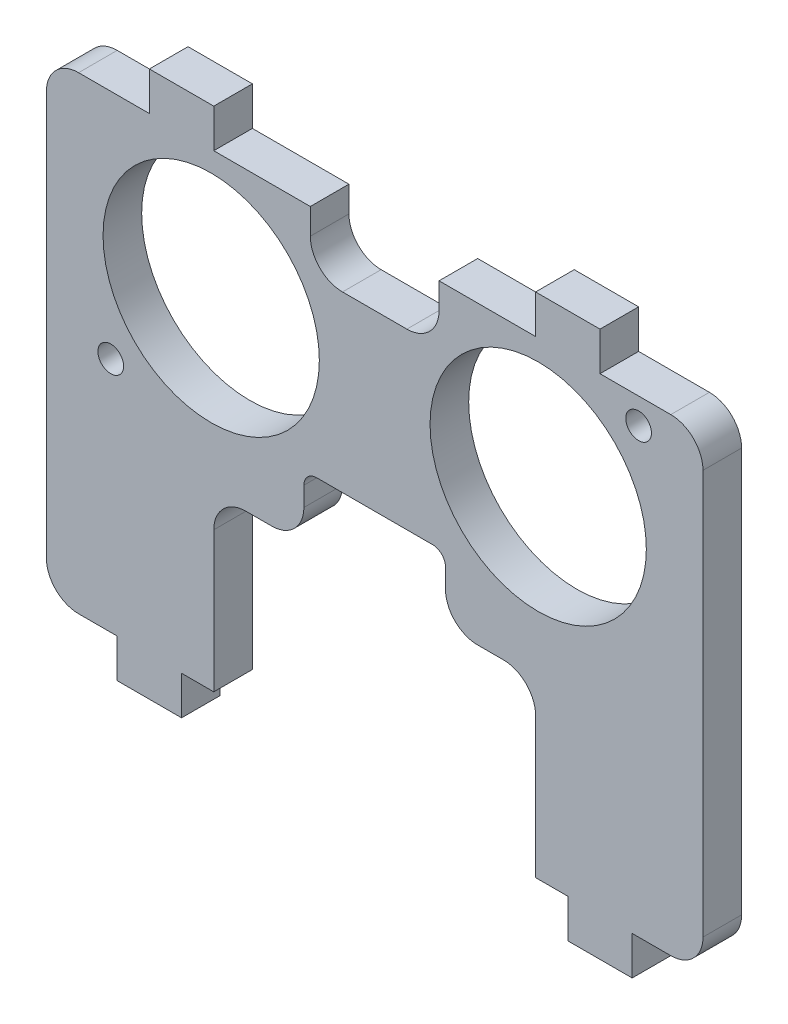
SolidWorks part; units mm, degrees
material "Beech"
ref_plane "Front Plane" through (0, 0, 0) normal (0, 0, 1) x (1, 0, 0)
ref_plane "Top Plane" through (0, 0, 0) normal (0, 1, 0) x (1, 0, 0)
ref_plane "Right Plane" through (0, 0, 0) normal (1, 0, 0) x (0, 0, -1)
sketch "Sketch1" plane through (0, 0, 0) normal (0, 0, 1) x (1, 0, 0)
  line L0 (-20.667, -16.4) -> (-20.667, 20)
  line L1 (-20.667, 20) -> (-15.667, 20)
  line L2 (24.333, 20) -> (24.333, -16.4)
  line L3 (24.333, -16.4) -> (21.833, -16.4)
  line L4 (14.333, -16.4) -> (14.333, -1)
  line L5 (13.333, 0) -> (7.333, 0)
  line L6 (-10.667, -1) -> (-10.667, -16.4)
  line L7 (-10.667, -16.4) -> (-13.167, -16.4)
  line L8 (1.833, 35.1) -> (1.833, -30.9857) construction
  line L9 (14.533, 10) -> (-10.867, 10) construction
  line L10 (-3.167, 20) -> (-3.167, 15.5)
  line L11 (-3.167, 15.5) -> (6.833, 15.5)
  line L12 (6.833, 15.5) -> (6.833, 20)
  line L13 (6.833, 20) -> (14.333, 20)
  line L14 (-20.667, 20) -> (24.333, 20) construction
  line L15 (-3.667, 2) -> (-3.667, 0)
  line L16 (-3.667, 2) -> (7.333, 2)
  line L17 (7.333, 2) -> (7.333, 0)
  line L18 (-3.667, 0) -> (-9.667, 0)
  line L19 (21.833, -16.4) -> (21.833, -19.4)
  line L20 (21.833, -19.4) -> (16.833, -19.4)
  line L21 (16.833, -19.4) -> (16.833, -16.4)
  line L22 (16.833, -16.4) -> (14.333, -16.4)
  line L23 (-18.167, -16.4) -> (-18.167, -19.4)
  line L24 (-13.167, -19.4) -> (-13.167, -16.4)
  line L25 (-18.167, -19.4) -> (-13.167, -19.4)
  line L26 (-18.167, -16.4) -> (-20.667, -16.4)
  line L27 (-15.667, 20) -> (-15.667, 23)
  line L28 (-15.667, 23) -> (-10.667, 23)
  line L29 (-10.667, 23) -> (-10.667, 20)
  line L30 (14.333, 23) -> (14.333, 20)
  line L31 (19.333, 23) -> (14.333, 23)
  line L32 (19.333, 20) -> (19.333, 23)
  line L33 (-10.667, 20) -> (-3.167, 20)
  line L34 (19.333, 20) -> (24.333, 20)
  circle A0 centre (22.333, 18) radius 1
  circle A1 centre (-18.667, 2) radius 1
  circle A2 centre (-10.867, 10) radius 8.4
  circle A3 centre (14.533, 10) radius 8.4
  arc A8 (13.333, 0) -> (14.333, -1) centre (13.333, -1) cw
  arc A9 (-9.667, 0) -> (-10.667, -1) centre (-9.667, -1) ccw
  point P21 (1.833, 10)
  point P24 (1.833, 15.5)
  point P29 (6.833, 15.5)
  point P32 (-3.167, 15.5)
  point P34 (-3.167, 20)
  point P37 (6.833, 20)
  point P42 (1.833, 20)
  point P47 (1.833, 2)
  point P53 (-3.667, 2)
  point P56 (-3.667, 0)
  dimension "D3" = 2
  dimension "D4" = 2
  dimension "D6" = 2
  dimension "D7" = 2
  dimension "D10" = 16.8
  dimension "D13" = 4.5
  dimension "D18" = 1
  dimension "D1" = 45
  dimension "D2" = 20
  dimension "D5" = 2
  dimension "D8" = 3
  dimension "D9" = 10
  dimension "D11" = 25.4
  dimension "D12" = 10
  dimension "D14" = 10
  dimension "D19" = 11
  dimension "D20" = 2
  dimension "D22" = 3
  dimension "D23" = 5
  dimension "D24" = 2.5
  dimension "D25" = 2.5
  dimension "D26" = 36.4
  dimension "D27" = 5
  dimension "D28" = 5
extrude "Boss-Extrude1" add sketch "Sketch1" along normal blind 3
sketch "Sketch2" plane through (0, 0, 3) normal (0, 0, 1) x (1, 0, 0)
  line L0 (-10.667, -3) -> (-3.667, -3)
  line L1 (-10.667, -16.4) -> (-10.667, -1) construction
  line L2 (-3.667, -3) -> (-3.667, 1)
  line L4 (7.333, 1) -> (7.333, -3)
  line L5 (7.333, -3) -> (14.333, -3)
  line L6 (14.333, -1) -> (14.333, -16.4) construction
  line L7 (-10.667, -3) -> (-10.667, 1)
  line L8 (-10.667, 1) -> (-3.667, 1)
  line L9 (-3.667, 0) -> (-3.667, 2) construction
  line L13 (7.333, 2) -> (7.333, 0) construction
  line L14 (7.333, 1) -> (14.333, 1)
  line L15 (14.333, 1) -> (14.333, -3)
  dimension "D1" = 4
extrude "Boss-Extrude2" add sketch "Sketch2" against normal up to surface (3 mm away) up to face at (-2.467, 10, 0)
ref_plane "Plane1" through (1.833, 0, 0) normal (1, 0, 0) x (0, 0, -1)
sketch "Sketch5" plane through (24.333, 0, 0) normal (1, 0, 0) x (0, 0, -1)
  line L1 (-3, -16.4) -> (0, -16.4)
  line L2 (-3, -16.4) -> (-3, 20)
  line L3 (-3, 20) -> (0, 20)
  line L4 (0, -16.4) -> (0, 20)
extrude "Boss-Extrude3" add sketch "Sketch5" along normal blind 3
mirror "Mirror1" about plane through (1.833, 0, 0) normal (1, 0, 0) of "Boss-Extrude3"
fillet "Fillet2" radius 2.5 10 edges at (6.833, 15.5, 1.5) (-3.167, 15.5, 1.5) (-10.667, -3, 1.5) (14.333, -3, 1.5) (7.333, -3, 1.5) (-3.667, -3, 1.5) (27.333, -16.4, 1.5) (27.333, 20, 1.5) (-23.667, 20, 1.5) (-23.667, -16.4, 1.5)
fillet "Fillet3" radius 1 2 edges at (7.333, 2, 1.5) (-3.667, 2, 1.5)
